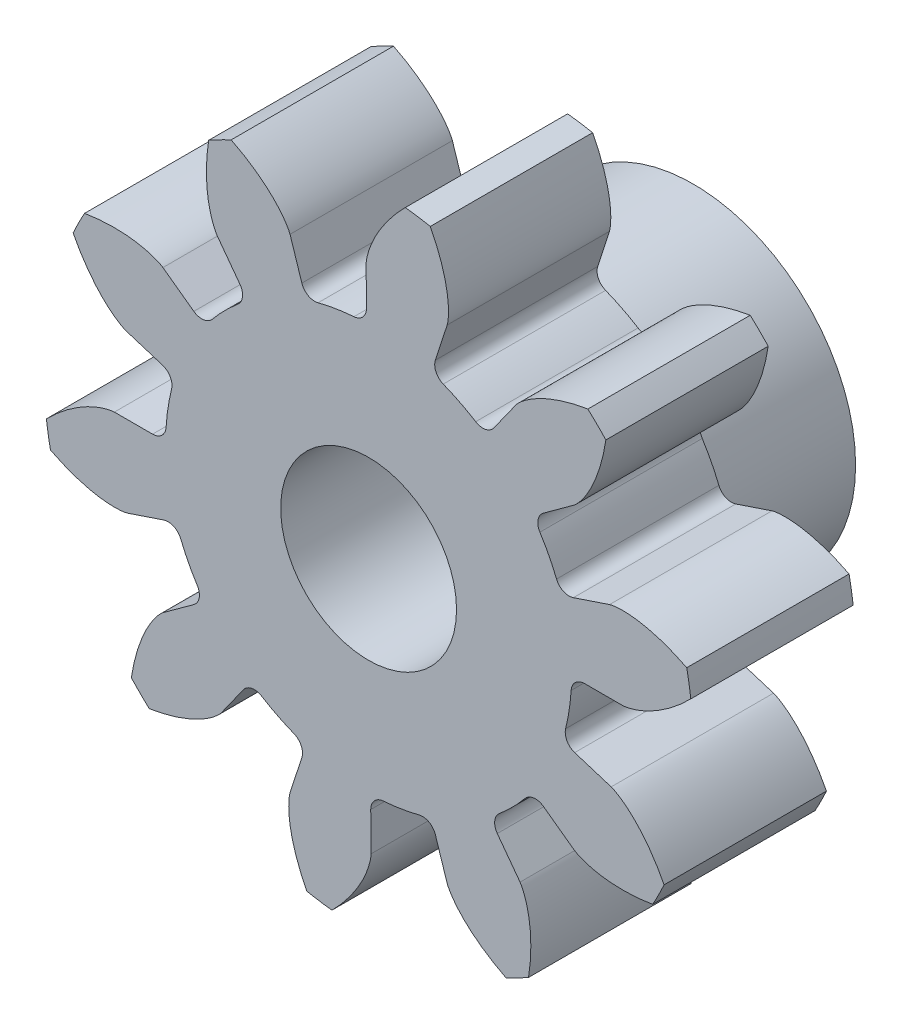
SolidWorks part; units mm, degrees
ref_plane "Front Plane" through (0, 0, 0) normal (0, 0, 1) x (1, 0, 0)
ref_plane "Top Plane" through (0, 0, 0) normal (0, 1, 0) x (1, 0, 0)
ref_plane "Right Plane" through (0, 0, 0) normal (1, 0, 0) x (0, 0, -1)
sketch "Sketch1" plane through (0, 0, 0) normal (0, 0, 1) x (1, 0, 0)
  line L0 (4.6985, 0) -> (3.75, 0)
  line L1 (5.9215, 0.9677) -> (-5.9215, -0.9677)
  line L2 (0, 0) -> (4.9994, 0.0745) construction
  circle A0 centre (0, 0) radius 4.6985 construction
  circle A1 centre (0, 0) radius 6
  circle A2 centre (0, 0) radius 3.75
  circle A3 centre (0, 0) radius 5 construction
  spline S0 degree 4 poles (4.6985, 0) (4.7019, 0.0001) (4.7117, 0.0005) (4.73, 0.0022) (4.7599, 0.0063) (4.7977, 0.0133) (4.8462, 0.0246) (4.9027, 0.0405) (4.9642, 0.0609) (5.0303, 0.086) (5.0954, 0.1137) (5.1594, 0.1437) (5.2224, 0.1758) (5.2977, 0.2172) (5.3864, 0.2702) (5.4878, 0.3372) (5.5997, 0.4188) (5.7102, 0.508) (5.8161, 0.6006) (5.9193, 0.6994) (6.0166, 0.7988) (6.1136, 0.9071) (6.2011, 1.0098) (6.2943, 1.1303) (6.3682, 1.2291) (6.4603, 1.365) (6.5131, 1.4469) (6.573, 1.5445) (6.5986, 1.5888) (6.6144, 1.6161) knots 0 0 0 0 0 0.005377 0.015084 0.028532 0.04661 0.064855 0.092111 0.119476 0.146842 0.174209 0.201575 0.228941 0.256307 0.307035 0.361767 0.4165 0.471232 0.525964 0.580697 0.635429 0.690161 0.744894 0.799626 0.854358 0.909091 0.954545 1 1 1 1 1 construction
  spline S1 degree 4 poles (4.6985, 0) (4.7019, 0.0001) (4.7117, 0.0005) (4.73, 0.0022) (4.7599, 0.0063) (4.7977, 0.0133) (4.8462, 0.0246) (4.9027, 0.0405) (4.9642, 0.0609) (5.0303, 0.086) (5.0954, 0.1137) (5.1594, 0.1437) (5.2224, 0.1758) (5.2977, 0.2172) (5.3864, 0.2702) (5.4878, 0.3372) (5.5997, 0.4188) (5.7102, 0.508) (5.8161, 0.6006) (5.9193, 0.6994) (6.0166, 0.7988) (6.1136, 0.9071) (6.2011, 1.0098) (6.2943, 1.1303) (6.3682, 1.2291) (6.4403, 1.3356) (6.4748, 1.388) (6.4922, 1.415) knots 0 0 0 0 0 0.005377 0.015084 0.028532 0.04661 0.064855 0.092111 0.119476 0.146842 0.174209 0.201575 0.228941 0.256307 0.307035 0.361767 0.4165 0.471232 0.525964 0.580697 0.635429 0.690161 0.744894 0.799626 0.854358 0.909091 0.909091 0.909091 0.909091 0.909091
  dimension "D1" = 9.3969
  dimension "D2" = 12
  dimension "D3" = 7.5
  dimension "D5" = 10
  dimension "D4" = 8.427
extrude "Boss-Extrude3" add sketch "Sketch1" along normal blind 3 contours L1 A2 | A2 L1 | L0 S1 A1 L1 A2
mirror "Mirror2" about plane through (0, 0, 3) normal (0.1613, -0.9869, 0) of "Boss-Extrude3"
fillet "Fillet1" radius 0.25 2 edges at (3.5549, 1.1937, 1.5) (3.75, 0, 1.5)
pattern_circular "CirPattern8" count 10 over 360 about axis through (0, 0, 3) along (0, 0, -1) of "Boss-Extrude3", "Mirror2", "Fillet1"
sketch "Sketch3" plane through (0, 0, 3) normal (0, 0, 1) x (1, 0, 0)
  circle A0 centre (0, 0) radius 1.625
  dimension "D1" = 3.25
extrude "Cut-Extrude2" cut sketch "Sketch3" against normal through all
sketch "Sketch4" plane through (0, 0, 0) normal (0, 0, -1) x (-1, 0, 0)
  circle A0 centre (0, 0) radius 1.625
  circle A1 centre (0, 0) radius 3
  dimension "D1" = 6
  dimension "D2" = 3.25
extrude "Boss-Extrude4" add sketch "Sketch4" along normal blind 3
sketch "Sketch5" plane through (0, 0, 0) normal (0, 1, 0) x (1, 0, 0)
  line L0 (0, 0) -> (0, 3) construction
  circle A0 centre (0, 3) radius 2.25
  dimension "D1" = 4.5
  dimension "D2" = 3
extrude "Cut-Extrude3" [suppressed] cut sketch "Sketch5" against normal through all both and the other way through all
fillet "Fillet2" [suppressed] radius 2
equation "\"d\"= 10'Pitch diameter"
equation "\"N\"= 10'Number of teeth"
equation "\"bl\"= 0.1mm'Backlash"
equation "\"pa\"= 20deg'Pressure angle (deg)"
equation "\"pc\"= ( 3.1415 * \"d\" ) / \"N\"\t'Circular pitch"
equation "\"m\"= \"d\" / \"N\"\t\t\t'module"
equation "\"P\"= \"N\" / \"d\"\t\t\t'Diametral pitch"
equation "\"a\"= 1/\"P\"\t\t\t'Addendum distance"
equation "\"b\"= 1.25 / \"P\"'Dedendum distance"
equation "\"rb\"= (\"d\"/2)*cos(\"pa\")\t\t'base circle radius"
equation "\"cp\"= 3.1415/\"P\"\t\t'Circular pitch"
equation "\"t\"= ( \"cp\" / 2 ) - \"bl\"'tooth tickness"
equation "\"c\"=\"b\"-\"a\"\t\t\t'Clearance"
equation "\"facewidth\"= 3'face width"
equation "\"rbd\"= \"rb\" * 2'base circle diameter"
equation "\"D1@Sketch1\"=\"rbd\""
equation "\"D2@Sketch1\"= \"d\" + (\"a\" * 2)"
equation "\"D3@Sketch1\" = \"ded\""
equation "\"D4@Sketch1\"= ((\"t\" /2) / (\"d\"/2)) * (180/3.1415)"
equation "\"D1@Boss-Extrude3\"=\"facewidth\""
equation "\"D1@Fillet1\"=\"c\""
equation "\"D1@CirPattern8\"=\"N\""
equation "\"D5@Sketch1\"=\"d\""
equation "\"ded1\"= \"d\" - 2 * ( ( ( \"d\" / 2 ) - \"rb\" ) + ( 0.5 * ( 1.25 / \"P\" ) ) )"
equation "\"ded2\"= \"d\" - ( \"b\" * 2 )"
equation "\"ded\"= IIF ( \"rb\" < ( \"ded2\" / 2 ) , \"ded1\" , \"ded2\" )"
equation "\"shaftdia\"= 3.25"
equation "\"D1@Sketch3\"=\"shaftdia\""
